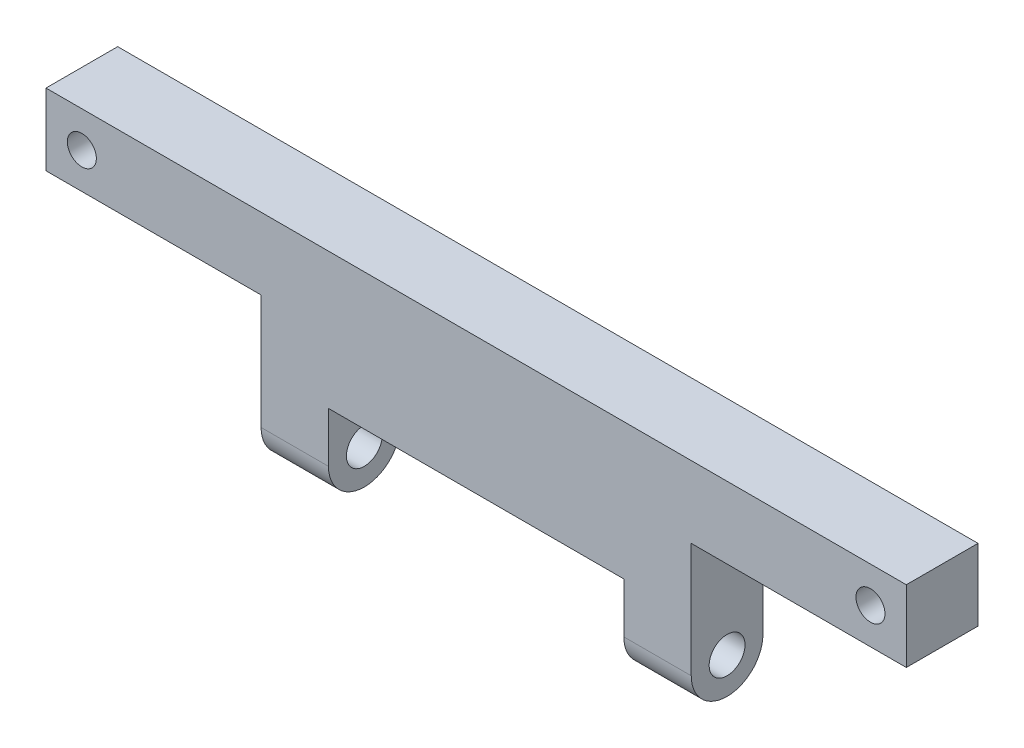
SolidWorks part; units mm, degrees
ref_plane "Front" through (0, 0, 0) normal (0, 0, 1) x (1, 0, 0)
ref_plane "Top" through (0, 0, 0) normal (0, 1, 0) x (1, 0, 0)
ref_plane "Right" through (0, 0, 0) normal (1, 0, 0) x (0, 0, -1)
sketch "Sketch1" plane through (0, 0, 0) normal (0, 0, 1) x (1, 0, 0)
  line L1 (0, 0) -> (20, 0)
  line L2 (0, 0) -> (0, 60)
  line L3 (0, 60) -> (20, 60)
  line L4 (20, 0) -> (20, 60)
  dimension "D1" = 60
  dimension "D2" = 20
extrude "Boss-Extrude1" add sketch "Sketch1" along normal blind 5
sketch "Sketch2" plane through (20, 0, 0) normal (1, 0, 0) x (0, 0, -1)
  line L0 (-5, 60) -> (0, 60) construction
  circle A0 centre (-2.5, 60) radius 2.5
  circle A1 centre (-2.5, 60) radius 1.25
  dimension "D1" = 2.5
extrude "Boss-Extrude2" add sketch "Sketch2" against normal up to surface (20 mm away) up to face at (0, 30, 2.5)
sketch "Sketch3" plane through (0, 0, 0) normal (-1, 0, 0) x (0, 0, 1)
  line L0 (3.75, 60) -> (1.25, 60) construction
  circle A0 centre (2.5, 60) radius 1.25
extrude "Cut-Extrude1" cut sketch "Sketch3" against normal blind 29
sketch "Sketch4" plane through (0, 0, 0) normal (-1, 0, 0) x (0, 0, 1)
  line L0 (5, 0) -> (0, 0) construction
  circle A0 centre (2.5, 0) radius 2.5
  circle A1 centre (2.5, 0) radius 1.25
  dimension "D1" = 2.5
extrude "Boss-Extrude3" add sketch "Sketch4" against normal up to surface (20 mm away) up to face at (20, 30.625, 2.5)
sketch "Sketch5" plane through (20, 0, 0) normal (1, 0, 0) x (0, 0, -1)
  line L0 (-3.75, 0) -> (-1.25, 0) construction
  circle A0 centre (-2.5, 0) radius 1.25
extrude "Cut-Extrude2" cut sketch "Sketch5" against normal blind 29
sketch "Sketch6" plane through (0, 0, 0) normal (-1, 0, 0) x (0, 0, 1)
  line L2 (5, 60) -> (5, 70)
  line L3 (5, 70) -> (0, 70)
  line L4 (0, 60) -> (0, 70)
  circle A0 centre (2.5, 60) radius 1.25
  arc A1 (0, 60) -> (5, 60) centre (2.5, 60) ccw
  dimension "D1" = 10
extrude "Boss-Extrude4" add sketch "Sketch6" along normal blind 30
sketch "Sketch7" plane through (0, 0, 0) normal (0, 0, -1) x (-1, 0, 0)
  line L1 (4.7, 63.5) -> (25.3, 63.5)
  line L2 (4.7, 63.5) -> (4.7, 56.5)
  line L3 (4.7, 56.5) -> (25.3, 56.5)
  line L4 (25.3, 63.5) -> (25.3, 56.5)
  line L6 (30, 70) -> (0, 70) construction
  point P4 (25.3, 60)
  point P5 (15, 63.5)
  point P9 (15, 70)
  dimension "D1" = 20.6
  dimension "D2" = 7
extrude "Cut-Extrude3" cut sketch "Sketch7" against normal blind 30
sketch "Sketch8" plane through (0, 0, 0) normal (-1, 0, 0) x (0, 0, 1)
  line L1 (-28.189, 70.3602) -> (32.3225, 70.3602)
  line L2 (-28.189, 70.3602) -> (-28.189, -8.2037)
  line L3 (-28.189, -8.2037) -> (32.3225, -8.2037)
  line L4 (32.3225, 70.3602) -> (32.3225, -8.2037)
extrude "Cut-Extrude4" cut sketch "Sketch8" against normal blind 41
sketch "Sketch10" plane through (0, 0, 0) normal (0, 0, -1) x (-1, 0, 0)
  line L0 (30, 70) -> (0, 70) construction
  line L1 (-15, 73) -> (45, 73)
  line L2 (-15, 73) -> (-15, 68)
  line L3 (-15, 68) -> (45, 68)
  line L4 (45, 73) -> (45, 68)
  point P4 (15, 68)
  point P7 (15, 70)
  point P8 (0, 0)
  dimension "D1" = 2
  dimension "D2" = 60
  dimension "D3" = 5
extrude "Boss-Extrude5" add sketch "Sketch10" against normal up to surface (5 mm away) up to face at (-15, 63.375, 5)
sketch "Sketch11" plane through (0, 0, 0) normal (0, 0, -1) x (-1, 0, 0)
  line L0 (45, 73) -> (-15, 73) construction
  line L1 (-15, 73) -> (-15, 68) construction
  line L2 (15, 73) -> (15, 84.1122)
  circle A0 centre (-12.5, 70.5) radius 1.0123
  circle A1 centre (42.5, 70.5) radius 1.0123
  dimension "D1" = 2.5
  dimension "D2" = 2.5
extrude "Cut-Extrude5" cut sketch "Sketch11" against normal blind 41 contours A0 | A1
